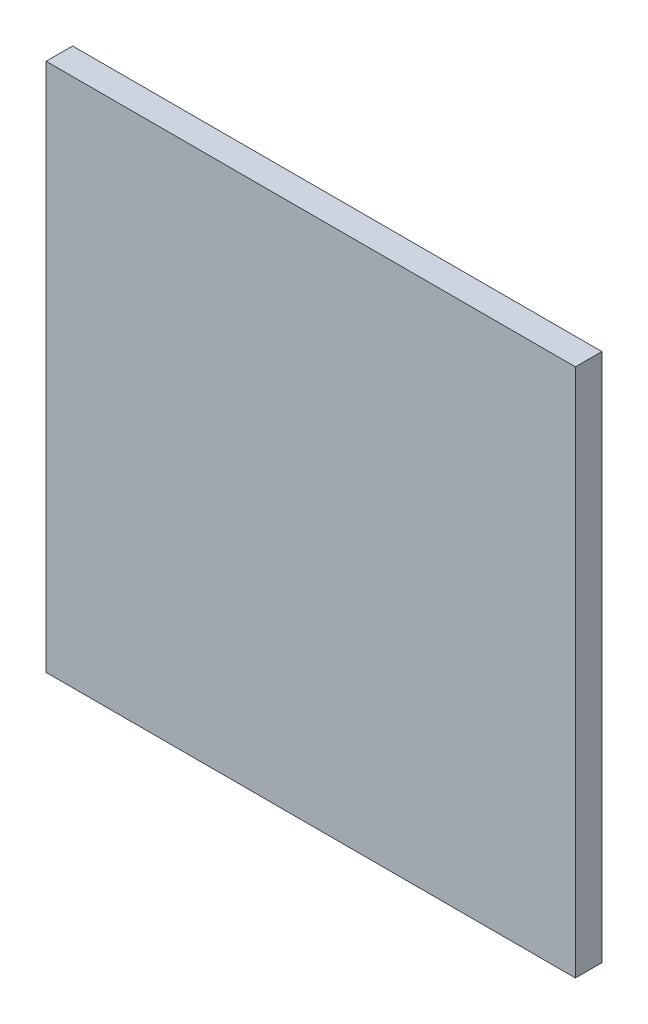
SolidWorks part; units mm, degrees
ref_plane "Front Plane" through (0, 0, 0) normal (1, 0, 0) x (0, 1, 0)
ref_plane "Top Plane" through (0, 0, 0) normal (0, 0, 1) x (0, 1, 0)
ref_plane "Right Plane" through (0, 0, 0) normal (0, 1, 0) x (-1, 0, 0)
sketch "Sketch1" plane through (0, 0, 0) normal (0, 0, 1) x (0, 1, 0)
  line L1 (0, 0) -> (25.4, 0)
  line L2 (0, 0) -> (0, 25.4)
  line L3 (0, 25.4) -> (25.4, 25.4)
  line L4 (25.4, 0) -> (25.4, 25.4)
  dimension "D1" = 25.4
  dimension "D2" = 25.4
extrude "Boss-Extrude1" add sketch "Sketch1" along normal blind 1.27
